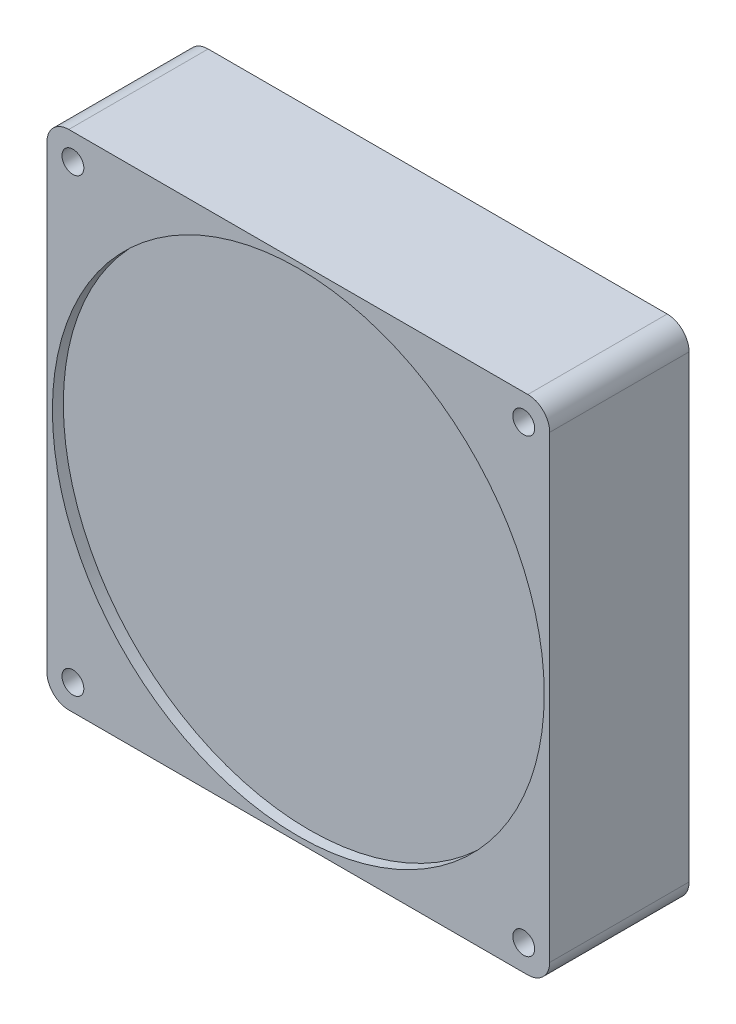
SolidWorks part; units mm, degrees
ref_plane "Front Plane" through (0, 0, 0) normal (0, 0, 1) x (1, 0, 0)
ref_plane "Top Plane" through (0, 0, 0) normal (0, 1, 0) x (1, 0, 0)
ref_plane "Right Plane" through (0, 0, 0) normal (1, 0, 0) x (0, 0, -1)
sketch "Sketch1" plane through (0, 0, 0) normal (0, 0, 1) x (1, 0, 0)
  line L1 (-46, -46) -> (46, -46)
  line L2 (-46, -46) -> (-46, 46)
  line L3 (-46, 46) -> (46, 46)
  line L4 (46, -46) -> (46, 46)
  line L5 (-46, -46) -> (46, 46) construction
  line L6 (-46, 46) -> (46, -46) construction
  point P0 (0, 0)
  dimension "D1" = 92
extrude "Boss-Extrude1" add sketch "Sketch1" along normal blind 25.5
sketch "Sketch2" plane through (0, 0, 25.5) normal (0, 0, 1) x (1, 0, 0)
  line L1 (41.25, -41.25) -> (-41.25, -41.25) construction
  line L2 (41.25, -41.25) -> (41.25, 41.25) construction
  line L3 (41.25, 41.25) -> (-41.25, 41.25) construction
  line L4 (-41.25, -41.25) -> (-41.25, 41.25) construction
  line L5 (41.25, -41.25) -> (-41.25, 41.25) construction
  line L6 (41.25, 41.25) -> (-41.25, -41.25) construction
  circle A0 centre (-41.25, 41.25) radius 2
  circle A1 centre (41.25, 41.25) radius 2
  circle A2 centre (41.25, -41.25) radius 2
  circle A3 centre (-41.25, -41.25) radius 2
  point P0 (0, 0)
  point P10 (43.25, 41.25)
  point P11 (39.25, 41.25)
  point P12 (-39.25, 41.25)
  point P13 (-43.25, 41.25)
  dimension "D2" = 4
  dimension "D1" = 78.5
  dimension "D3" = 86.5
extrude "Cut-Extrude1" cut sketch "Sketch2" against normal through all
fillet "Fillet1" radius 4 4 edges at (-46, -46, 12.75) (46, -46, 12.75) (46, 46, 12.75) (-46, 46, 12.75)
sketch "Sketch3" plane through (0, 0, 25.5) normal (0, 0, 1) x (1, 0, 0)
  circle A0 centre (0, 0) radius 45
  dimension "D1" = 90
extrude "Cut-Extrude2" cut sketch "Sketch3" against normal blind 2
sketch "Sketch4" plane through (0, 0, 0) normal (0, 0, -1) x (-1, 0, 0)
  circle A1 centre (0, 0) radius 45
  circle A2 centre (0, 0) radius 45
  dimension "D1" = 0
extrude "Cut-Extrude3" cut sketch "Sketch4" against normal blind 2
